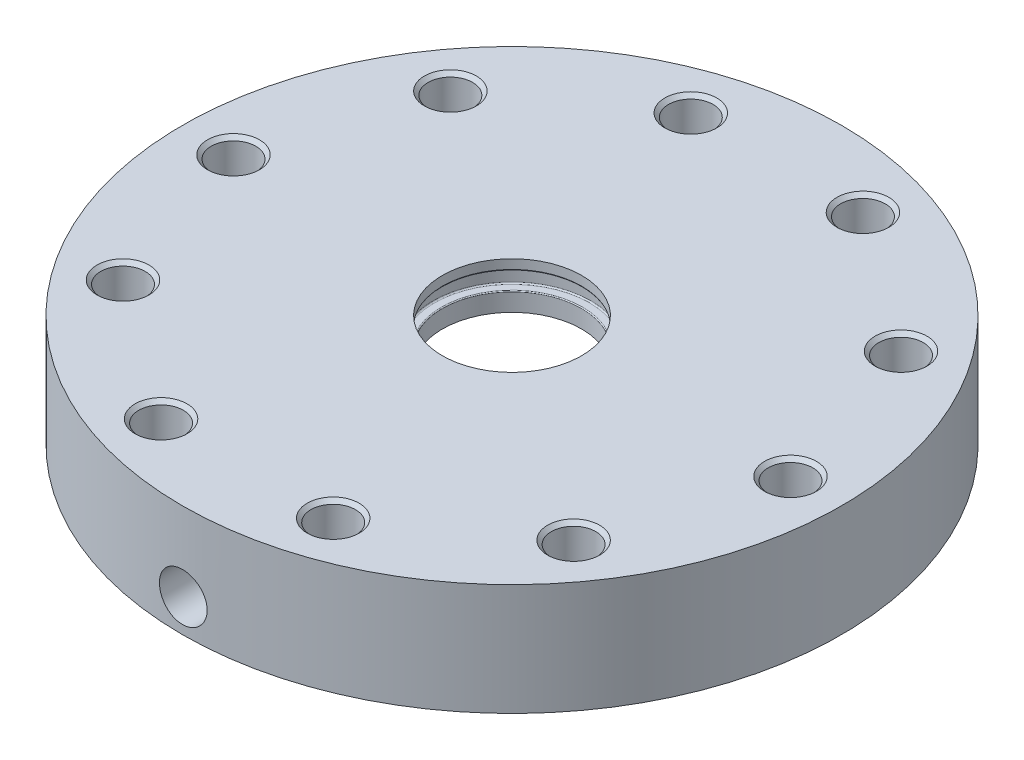
SolidWorks part; units mm, degrees
material "Inconel 718"
ref_plane "Front Plane" through (0, 0, 0) normal (0, 0, 1) x (1, 0, 0)
ref_plane "Top Plane" through (0, 0, 0) normal (0, 1, 0) x (1, 0, 0)
ref_plane "Right Plane" through (0, 0, 0) normal (1, 0, 0) x (0, 0, -1)
sketch "Sketch1" plane through (0, 0, 0) normal (0, 0, 1) x (1, 0, 0)
  line L0 (0, 0) -> (0, 20.7162) construction
  line L1 (9.525, 0) -> (45.085, 0)
  line L2 (9.525, 0) -> (9.525, -6.35)
  line L3 (9.525, -6.35) -> (24.13, -6.35)
  line L6 (24.13, -6.35) -> (24.13, -15.2654)
  line L7 (24.13, -15.2654) -> (45.085, -15.2654)
  line L8 (45.085, -15.2654) -> (45.085, 0)
  dimension "D1" = 6.35
  dimension "D2" = 9.525
  dimension "D4" = 8.9154
  dimension "D5" = 24.13
  dimension "D6" = 45.085
revolve "Revolve1" add sketch "Sketch1" angle 360 about L0
hole_wizard "Hole1" positions "Sketch2" profile "Sketch3" legacy
sketch "Sketch2" plane through (0, 0, 0) normal (0, 1, 0) x (1, 0, 0)
  line L0 (0, 0) -> (38.1, 0) construction
  point P0 (38.1, 0)
  dimension "D1" = 38.1
sketch "Sketch3" plane through (38.1, 0, 0) normal (1, 0, 0) x (0, 0, 1)
  line L0 (0, 0) -> (0, 15.2654)
  line L1 (0, 15.2654) -> (3.048, 15.2654)
  line L2 (3.048, 15.2654) -> (3.048, 0)
  line L5 (3.048, 0) -> (0, 0)
  line L11 (0, -6.35) -> (0, 107.95) construction
  dimension "Thru Hole Dia." = 6.096
  dimension "Thru Hole Depth" = 15.2654
pattern_circular "CirPattern1" count 10 over 360 about axis through (0, 0, 0) along (0, 1, 0) of "Hole1"
fillet "Fillet1" radius 1.27 1 edges at (0, -6.35, -24.13)
sketch "Sketch5" plane through (0, 0, 0) normal (0, 1, 0) x (1, 0, 0)
  line L0 (0, 0) -> (-11.7735, -36.2353)
  line L1 (11.7735, -36.2353) -> (-11.7735, -36.2353)
  line L2 (11.7735, -36.2353) -> (0, 0)
  line L3 (0, 0) -> (0, -36.2353)
  line L4 (0, -36.2353) -> (0, -45.085)
  line L5 (0, -45.085) -> (0, -34.925)
  circle A0 centre (0, 0) radius 45.085 construction
  circle A1 centre (0, 0) radius 9.525 construction
  arc A2 (-2.9434, -9.0588) -> (2.9434, -9.0588) centre (0, 0) ccw
  dimension "D1" = 10.16
ref_plane "Plane1" through (0, 0, 45.085) normal (0, 0, 1) x (1, 0, 0)
sketch "Sketch9" plane through (0, 0, 45.085) normal (0, 0, 1) x (1, 0, 0)
  line L0 (0, 0) -> (0, -10.795)
hole_wizard "5/16-18 Tapped Hole1" positions "Sketch10" profile "Sketch11" tap size "5/16-18" standard "ANSI Inch"
sketch "Sketch10" plane through (0, 0, 45.085) normal (0, 0, 1) x (1, 0, 0)
  point P0 (0, -10.795)
cosmetic thread "Hole Thread2" parameters "D1"=10.16, "D2"=7.9375
sketch "Sketch11" plane through (0, -10.795, 45.085) normal (1, 0, 0) x (0, -1, 0)
  line L0 (0, 0) -> (0, 12.1211)
  line L1 (0, 12.1211) -> (3.2639, 10.16)
  line L2 (3.2639, 10.16) -> (3.2639, 0)
  line L5 (3.2639, 0) -> (0, 0)
  line L10 (0, 12.1211) -> (-3.2639, 10.16) construction
  line L11 (0, -6.35) -> (0, 107.95) construction
  dimension "Tap Drill Dia." = 6.5278
  dimension "Tap Drill Depth" = 10.16
  dimension "Drill Angle" = 118
ref_plane "Plane2" through (0, 0, 34.925) normal (0, 0, 1) x (1, 0, 0)
hole_wizard "1/8 (0.125) Diameter Hole1" positions "Sketch16" profile "Sketch18" hole size "1/8" standard "ANSI Inch"
sketch "Sketch16" plane through (0, 0, 34.925) normal (0, 0, 1) x (1, 0, 0)
  point P0 (0, -10.795)
sketch "Sketch18" plane through (0, -10.795, 34.925) normal (1, 0, 0) x (0, -1, 0)
  line L0 (0, 0) -> (0, 15.9399)
  line L1 (0, 15.9399) -> (1.5875, 14.986)
  line L2 (1.5875, 14.986) -> (1.5875, 0)
  line L5 (1.5875, 0) -> (0, 0)
  line L10 (0, 15.9399) -> (-1.5875, 14.986) construction
  line L11 (0, -6.35) -> (0, 107.95) construction
  dimension "Hole Dia." = 3.175
  dimension "Hole Depth" = 14.986
  dimension "Drill Angle" = 118
sketch "Sketch20" plane through (0, 0, 0) normal (0, 0, 1) x (1, 0, 0)
  line L0 (0, 0) -> (0, 12.2553) construction
  line L1 (9.525, -1.397) -> (9.525, -3.81)
  line L2 (45.085, 0) -> (-45.085, 0) construction
  line L3 (45.085, 0) -> (-45.085, 0) construction
  line L6 (9.525, -1.397) -> (10.795, -1.397)
  line L7 (10.795, -1.397) -> (10.795, -3.81)
  line L8 (10.795, -3.81) -> (9.525, -3.81)
  point P1 (9.525, -2.6035)
  point P2 (10.795, -2.6035)
  dimension "D1" = 2.413
  dimension "D2" = 10.795
  dimension "D3" = 9.525
  dimension "D4" = 1.397
revolve "Cut-Revolve1" cut sketch "Sketch20" angle 360 about L0
fillet "Fillet2" radius 0.1778 2 edges at (0, -1.397, -10.795) (0, -3.81, -10.795)
fillet "Fillet3" radius 0.127 2 edges at (0, -3.81, -9.525) (0, -1.397, -9.525)
chamfer "Chamfer1" distance 0.508 angle 45 20 edges at (11.7735, -15.2654, 39.2833) (11.7735, 0, 39.2833) (38.1, -15.2654, 3.048) (38.1, 0, 3.048) (30.8235, 0, -19.3466) (30.8235, -15.2654, -19.3466) (11.7735, 0, -33.1873) (11.7735, -15.2654, -33.1873) (-11.7735, 0, -33.1873) (-11.7735, -15.2654, -33.1873) (-30.8235, 0, -19.3466) (-30.8235, -15.2654, -19.3466) (-38.1, 0, 3.048) (-38.1, -15.2654, 3.048) (-30.8235, 0, 25.4426) (-30.8235, -15.2654, 25.4426) (-11.7735, 0, 39.2833) (-11.7735, -15.2654, 39.2833) (30.8235, 0, 25.4426) (30.8235, -15.2654, 25.4426)
